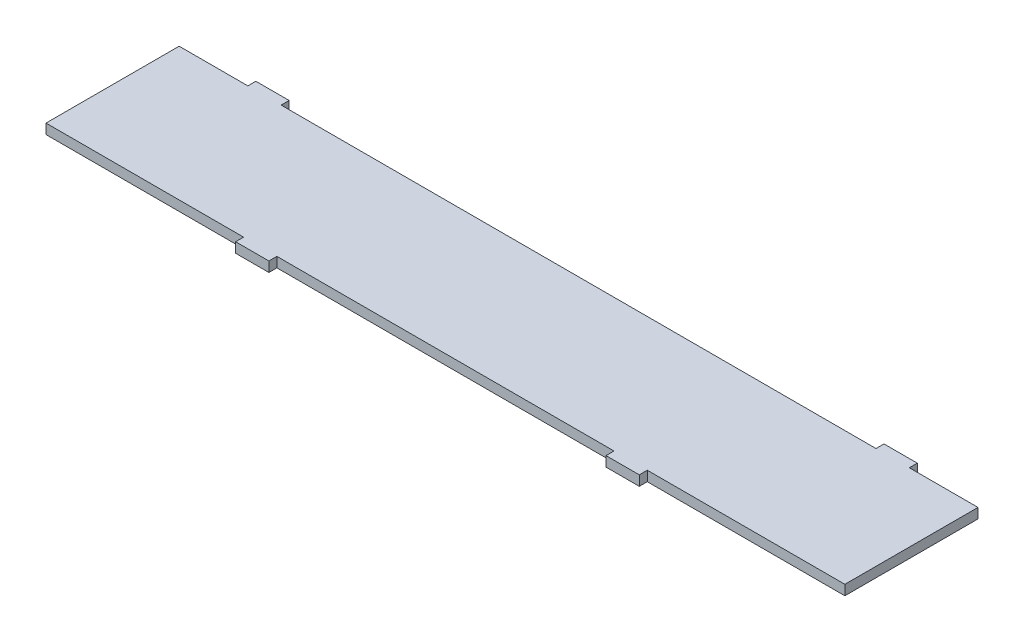
SolidWorks part; units mm, degrees
ref_plane "Alzado" through (0, 0, 0) normal (0, 0, 1) x (1, 0, 0)
ref_plane "Planta" through (0, 0, 0) normal (0, 1, 0) x (1, 0, 0)
ref_plane "Vista lateral" through (0, 0, 0) normal (1, 0, 0) x (0, 0, -1)
sketch "Croquis1" plane through (0, 0, 0) normal (0, 1, 0) x (1, 0, 0)
  line L1 (-600, -100) -> (600, -100)
  line L2 (-600, -100) -> (-600, 100)
  line L3 (-600, 100) -> (600, 100)
  line L4 (600, -100) -> (600, 100)
  line L5 (-600, -100) -> (600, 100) construction
  line L6 (-600, 100) -> (600, -100) construction
  point P0 (0, 0)
  dimension "D1" = 1200
  dimension "D2" = 200
extrude "Saliente-Extruir1" add sketch "Croquis1" along normal blind 15
sketch "Croquis3" plane through (0, 0, 0) normal (0, 1, 0) x (1, 0, 0)
  line L0 (600, 100) -> (-600, 100) construction
  line L1 (-400, 100) -> (-350, 100) construction
  line L2 (-400, 100) -> (-400, 115) construction
  line L3 (-400, 115) -> (-350, 115) construction
  line L4 (-350, 100) -> (-350, 115) construction
  line L5 (0, 0) -> (0, 251.2938) construction
  line L6 (0, 0) -> (-600, 0) construction
  line L7 (-600, 100) -> (-600, -100) construction
  line L20 (446.8, 112) -> (496.8, 112)
  line L21 (-446.8, 100) -> (-496.8, 100)
  line L22 (-446.8, 100) -> (-446.8, 112)
  line L23 (-446.8, 112) -> (-496.8, 112)
  line L24 (-496.8, 100) -> (-496.8, 112)
  line L25 (446.8, 100) -> (446.8, 112)
  line L26 (446.8, 100) -> (496.8, 100)
  line L27 (496.8, 100) -> (496.8, 112)
  line L28 (-600, -100) -> (600, -100) construction
  line L29 (-303.2, -100) -> (-253.2, -100)
  line L30 (-303.2, -100) -> (-303.2, -112)
  line L31 (-303.2, -112) -> (-253.2, -112)
  line L32 (-253.2, -100) -> (-253.2, -112)
  line L33 (303.2, -100) -> (303.2, -112)
  line L34 (253.2, -100) -> (253.2, -112)
  line L35 (303.2, -100) -> (253.2, -100)
  line L36 (303.2, -112) -> (253.2, -112)
  point P9 (-375, 100)
  dimension "D1" = 15
  dimension "D2" = 50
  dimension "D3" = 375
  dimension "D4" = 46.8
  dimension "D5" = 50
  dimension "D6" = 12
  dimension "D7" = 12
  dimension "D8" = 50
  dimension "D9" = 46.8
extrude "Saliente-Extruir2" add sketch "Croquis3" along normal blind 15
